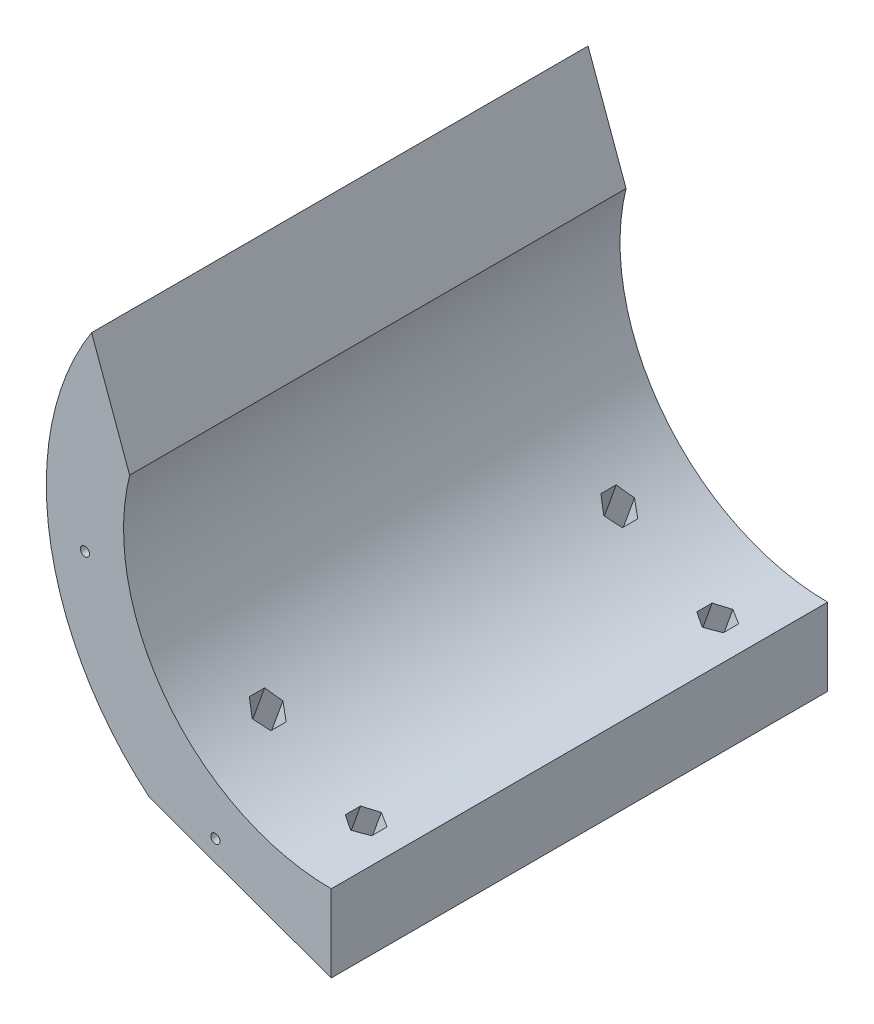
SolidWorks part; units mm, degrees
ref_plane "Front Plane" through (0, 0, 0) normal (0, 0, 1) x (1, 0, 0)
ref_plane "Top Plane" through (0, 0, 0) normal (0, 1, 0) x (1, 0, 0)
ref_plane "Right Plane" through (0, 0, 0) normal (1, 0, 0) x (0, 0, -1)
sketch "Sketch1" plane through (0, 0, 0) normal (0, 0, 1) x (1, 0, 0)
  line L0 (0, 59) -> (0, 43)
  line L1 (0, -43) -> (0, -59)
  arc A0 (0, 43) -> (0, -43) centre (0, 0) ccw
  arc A1 (0, 59) -> (0, -59) centre (0, 0) ccw
  dimension "D1" = 86
  dimension "D2" = 118
extrude "Boss-Extrude1" add sketch "Sketch1" along normal blind 102.8
sketch "Sketch3" plane through (0, 0, 102.8) normal (0, 0, 1) x (1, 0, 0)
  line L3 (0, 0) -> (0, 90)
  line L4 (0, 90) -> (-70.7573, 90)
  line L5 (-70.7573, 90) -> (-38, 0)
  line L6 (-38, 0) -> (0, 0)
  dimension "D1" = 90
  dimension "D2" = 38
  dimension "D3" = 110
extrude "Cut-Extrude1" cut sketch "Sketch3" against normal through all
sketch "Sketch4" plane through (0, 0, 102.8) normal (0, 0, 1) x (1, 0, 0)
  line L0 (0, -59) -> (-37.6317, -45.4407)
  line L1 (-37.6317, -45.4407) -> (-42.5173, -59)
  line L2 (-42.5173, -59) -> (0, -59)
  arc A0 (-49.6186, 31.9217) -> (0, -59) centre (0, 0) ccw construction
  dimension "D1" = 40
extrude "Cut-Extrude2" cut sketch "Sketch4" against normal through all
sketch "Sketch5" plane through (-18.8158, -52.2203, 0) normal (-0.339, -0.9408, 0) x (0.9408, -0.339, 0)
  line L0 (20, 51.4) -> (-20, 51.4) construction
  line L1 (20, 102.8) -> (20, 0) construction
  line L2 (-20, 0) -> (-20, 102.8) construction
  line L3 (20, 0) -> (-20, 0) construction
  circle A0 centre (7, 15) radius 1.65
  circle A1 centre (-15.5, 15) radius 1.65
  circle A2 centre (-15.5, 87.8) radius 1.65
  circle A3 centre (7, 87.8) radius 1.65
  dimension "D1" = 3.3
  dimension "D3" = 3.3
  dimension "D2" = 13
  dimension "D4" = 22.5
  dimension "D5" = 15
extrude "Cut-Extrude3" cut sketch "Sketch5" against normal up to next
sketch "Sketch6" plane through (-18.8158, -52.2203, 0) normal (-0.339, -0.9408, 0) x (0.9408, -0.339, 0)
  line L0 (20, 51.4) -> (-20, 51.4) construction
  line L1 (7, 11.8246) -> (9.75, 13.4123)
  line L2 (9.75, 13.4123) -> (9.75, 16.5877)
  line L3 (9.75, 16.5877) -> (7, 18.1754)
  line L4 (7, 18.1754) -> (4.25, 16.5877)
  line L5 (4.25, 16.5877) -> (4.25, 13.4123)
  line L6 (4.25, 13.4123) -> (7, 11.8246)
  line L7 (-15.5, 11.8246) -> (-12.75, 13.4123)
  line L8 (-12.75, 13.4123) -> (-12.75, 16.5877)
  line L9 (-12.75, 16.5877) -> (-15.5, 18.1754)
  line L10 (-15.5, 18.1754) -> (-18.25, 16.5877)
  line L11 (-18.25, 16.5877) -> (-18.25, 13.4123)
  line L12 (-18.25, 13.4123) -> (-15.5, 11.8246)
  line L13 (20, 102.8) -> (20, 0) construction
  line L14 (-20, 0) -> (-20, 102.8) construction
  line L15 (-18.25, 89.3877) -> (-15.5, 90.9754)
  line L16 (-18.25, 86.2123) -> (-18.25, 89.3877)
  line L17 (-15.5, 84.6246) -> (-18.25, 86.2123)
  line L18 (-12.75, 86.2123) -> (-15.5, 84.6246)
  line L19 (-12.75, 89.3877) -> (-12.75, 86.2123)
  line L20 (-15.5, 90.9754) -> (-12.75, 89.3877)
  line L21 (4.25, 89.3877) -> (7, 90.9754)
  line L22 (4.25, 86.2123) -> (4.25, 89.3877)
  line L23 (7, 84.6246) -> (4.25, 86.2123)
  line L24 (9.75, 86.2123) -> (7, 84.6246)
  line L25 (9.75, 89.3877) -> (9.75, 86.2123)
  line L26 (7, 90.9754) -> (9.75, 89.3877)
  circle A0 centre (7, 15) radius 2.75 construction
  circle A1 centre (-15.5, 15) radius 2.75 construction
  circle A2 centre (-15.5, 87.8) radius 2.75 construction
  circle A3 centre (7, 87.8) radius 2.75 construction
  dimension "D1" = 5.5
  dimension "D2" = 5.5
extrude "Cut-Extrude4" cut sketch "Sketch6" against normal through all from offset 5 offset against normal yes
sketch "Sketch7" plane through (0, 0, 0) normal (0, 0, -1) x (-1, 0, 0)
  line L0 (0, -59) -> (0, -43) construction
  circle A0 centre (24, -46) radius 0.95
  circle A1 centre (51, -8) radius 0.95
  dimension "D1" = 1.9
  dimension "D2" = 1.9
  dimension "D3" = 24
  dimension "D4" = 13
  dimension "D5" = 51
  dimension "D6" = 51
extrude "Cut-Extrude5" cut sketch "Sketch7" against normal through all
